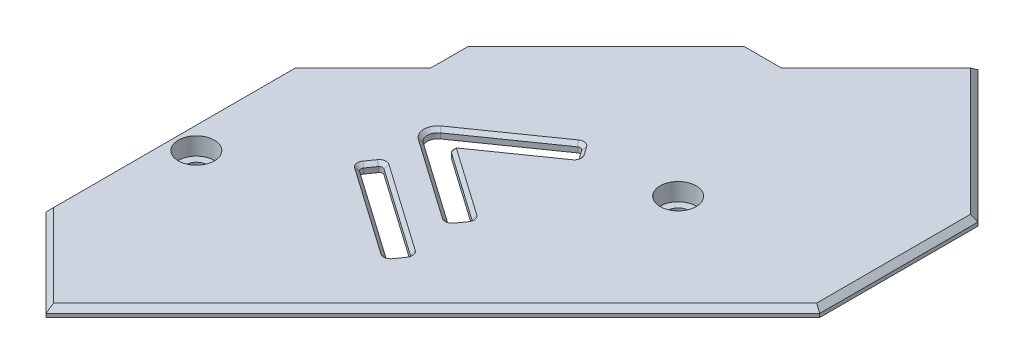
SolidWorks part; units mm, degrees
ref_plane "前视基准面" through (0, 0, 0) normal (0, 0, 1) x (1, 0, 0)
ref_plane "上视基准面" through (0, 0, 0) normal (0, 1, 0) x (1, 0, 0)
ref_plane "右视基准面" through (0, 0, 0) normal (1, 0, 0) x (0, 0, -1)
sketch "草图1" plane through (0, 0, 0) normal (0, 1, 0) x (1, 0, 0)
  line L0 (0, 0) -> (44, 44)
  line L1 (44, 44) -> (44, 62)
  line L2 (44, 62) -> (29, 77)
  line L3 (29, 77) -> (18, 66)
  line L4 (-10, 38) -> (-10, 10)
  line L5 (-10, 10) -> (0, 0)
  line L6 (0, 0) -> (50.7921, 0) construction
  line L7 (-2.3, 45.7) -> (-2.3, 49.9426)
  line L8 (-2.3, 49.9426) -> (13.7574, 66)
  line L9 (13.7574, 66) -> (18, 66)
  line L10 (-2.3, 45.7) -> (-10, 38)
  dimension "D1" = 45
  dimension "D2" = 44
  dimension "D3" = 10
  dimension "D4" = 15
  dimension "D5" = 77
  dimension "D6" = 2.3
  dimension "D7" = 66
  dimension "D8" = 3
extrude "凸台-拉伸1" add sketch "草图1" along normal blind 1
chamfer "倒角1" distance 0.6 angle 45 10 edges at (36.5, 1, -69.5) (-5, 1, -5) (-10, 1, -24) (23.5, 1, -71.5) (44, 1, -53) (-6.15, 1, -41.85) (-2.3, 1, -47.8213) (5.7287, 1, -57.9713) (15.8787, 1, -66) (22, 1, -22)
sketch "草图2" plane through (0, 0, 0) normal (0, -1, 0) x (1, 0, 0)
  line L1 (-10, -21) -> (-4, -21)
  line L2 (-10, -21) -> (-10, -27)
  line L3 (-10, -27) -> (-4, -27)
  line L4 (-4, -21) -> (-4, -27)
  line L5 (22, -44) -> (28, -44)
  line L6 (22, -44) -> (22, -50)
  line L7 (22, -50) -> (28, -50)
  line L8 (28, -44) -> (28, -50)
  dimension "D1" = 4
  dimension "D2" = 21
  dimension "D3" = 6
  dimension "D4" = 6
  dimension "D5" = 44
  dimension "D6" = 6
  dimension "D7" = 6
  dimension "D8" = 22
extrude "凸台-拉伸2" add sketch "草图2" along normal blind 3
sketch "草图3" plane through (0, -3, 0) normal (0, -1, 0) x (-1, 0, 0)
  circle A0 centre (6.9, 24) radius 1.2
  circle A1 centre (-25, 46.9) radius 1.2
  dimension "D1" = 2.4
  dimension "D2" = 2.4
extrude "切除-拉伸1" cut sketch "草图3" against normal through all
sketch "草图4" plane through (0, 1, 0) normal (0, 1, 0) x (1, 0, 0)
  circle A0 centre (-6.9, 24) radius 2.05
  circle A1 centre (25, 46.9) radius 2.05
  dimension "D1" = 4.1
  dimension "D2" = 4.1
extrude "切除-拉伸2" cut sketch "草图4" against normal blind 2
fillet "圆角1" radius 2 6 edges at (-4, -1.5, -21) (-4, -1.5, -27) (22, -1.5, -50) (28, -1.5, -50) (28, -1.5, -44) (22, -1.5, -44)
sketch "草图5" plane through (0, 1, 0) normal (0, 1, 0) x (1, 0, 0)
  line L0 (14.3528, 24.4) -> (15.5, 26.0383)
  line L1 (2.5, 24.4) -> (15.5, 24.4) construction
  line L2 (2.5, 24.4) -> (2.5, 46.6766) construction
  line L3 (2.5, 46.6766) -> (15.5, 46.6766) construction
  line L4 (15.5, 24.4) -> (15.5, 46.6766) construction
  line L5 (14.3528, 24.4) -> (3.7039, 31.8565)
  line L6 (15.5, 26.0383) -> (4.851, 33.4948)
  line L7 (3.7039, 31.8565) -> (4.851, 33.4948)
  line L8 (14.3528, 31.4) -> (3.4442, 39.0383)
  line L9 (3.4442, 39.0383) -> (14.3528, 46.6766)
  line L10 (14.3528, 46.6766) -> (15.5, 45.0383)
  line L11 (15.5, 45.0383) -> (6.9311, 39.0383)
  line L12 (6.9311, 39.0383) -> (15.5, 33.0383)
  line L13 (15.5, 33.0383) -> (14.3528, 31.4)
  dimension "D1" = 2
  dimension "D2" = 55
  dimension "D3" = 55
  dimension "D4" = 0
  dimension "D5" = 0
  dimension "D6" = 0
  dimension "D7" = 13
  dimension "D8" = 7
  dimension "D9" = 2
  dimension "D10" = 2
  dimension "D11" = 90
  dimension "D12" = 12
  dimension "D13" = 0
  dimension "D14" = 0
  dimension "D15" = 13
  dimension "D16" = 24.4
  dimension "D17" = 15.5
extrude "切除-拉伸3" cut sketch "草图5" against normal through all
fillet "圆角2" radius 0.4 9 edges at (6.9311, 0.5, -39.0383) (14.3528, 0.5, -46.6766) (15.5, 0.5, -45.0383) (15.5, 0.5, -33.0383) (14.3528, 0.5, -31.4) (15.5, 0.5, -26.0383) (14.3528, 0.5, -24.4) (4.851, 0.5, -33.4948) (3.7039, 0.5, -31.8565)
fillet "圆角3" radius 1.2 1 edges at (3.4442, 0.5, -39.0383)
chamfer "倒角2" distance 0.4 angle 45 20 edges at (4.2774, 1, -32.6756) (9.4366, 1, -43.2342) (3.867, 1, -31.8853) (9.0284, 1, -28.1282) (14.3241, 1, -24.5632) (14.9264, 1, -25.2192) (15.3368, 1, -26.0095) (10.1755, 1, -29.7666) (4.8798, 1, -33.3316) (14.9264, 1, -45.8575) (14.3241, 1, -46.5134) (15.3368, 1, -45.0671) (11.2857, 1, -42.0874) (7.2285, 1, -39.0383) (11.2857, 1, -35.9892) (15.3368, 1, -33.0095) (14.9264, 1, -32.2192) (14.3241, 1, -31.5632) (9.4366, 1, -34.8424) (4.3364, 1, -39.0383)
